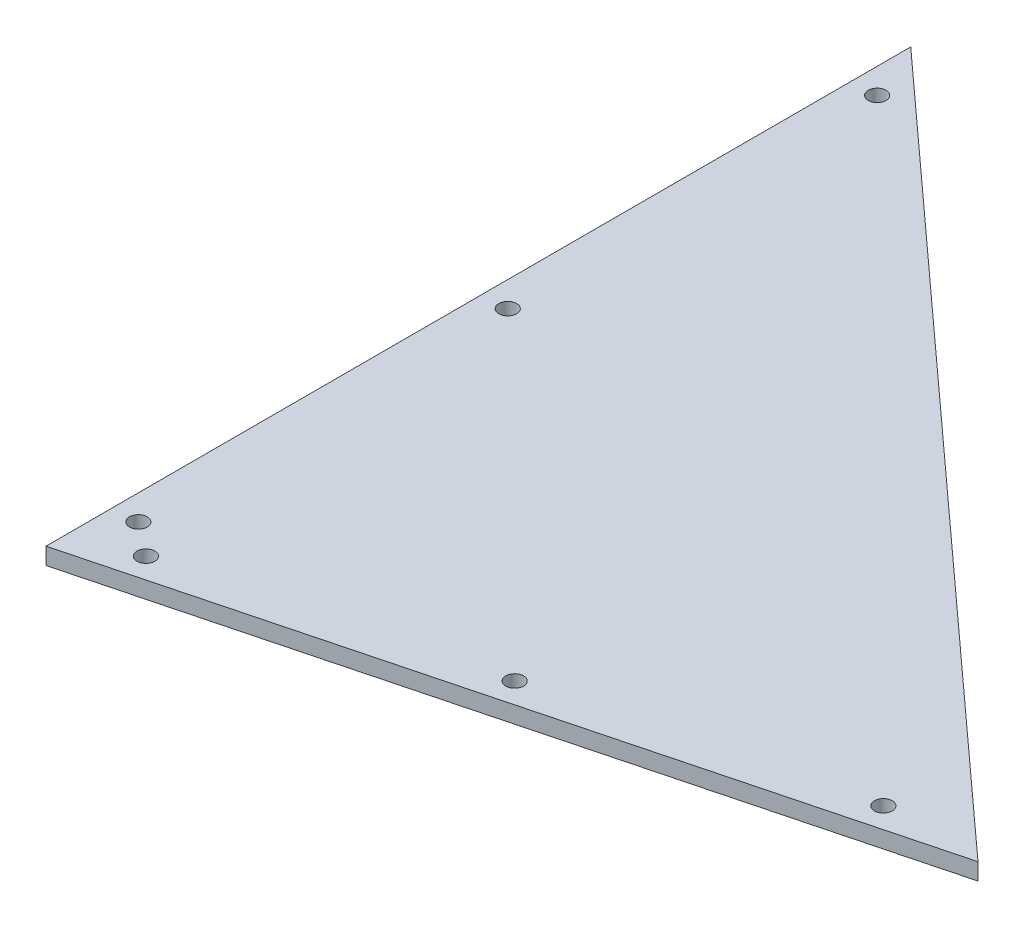
SolidWorks part; units mm, degrees
material "PC High Viscosity"
ref_plane "Front Plane" through (0, 0, 0) normal (0, 0, 1) x (1, 0, 0)
ref_plane "Top Plane" through (0, 0, 0) normal (0, 1, 0) x (1, 0, 0)
ref_plane "Right Plane" through (0, 0, 0) normal (1, 0, 0) x (0, 0, -1)
sketch "Sketch1" plane through (0, 0, 0) normal (0, 1, 0) x (1, 0, 0)
  line L0 (0, 0) -> (0, 327.025)
  line L1 (0, 327.025) -> (279.5805, 72.8863)
  line L2 (279.5805, 72.8863) -> (0, 0)
  dimension "D1" = 327.025
  dimension "D2" = 377.825
  dimension "D3" = 288.925
extrude "Boss-Extrude1" add sketch "Sketch1" along normal blind 6.35
sketch "Sketch2" plane through (0, 6.35, 0) normal (0, 1, 0) x (1, 0, 0)
  line L0 (22.1757, 15.6245) -> (243.3822, 73.2928) construction
  line L1 (9.525, 25.4) -> (9.525, 304.8) construction
  line L2 (0, 0) -> (279.5805, 72.8863) construction
  line L3 (0, 327.025) -> (0, 0) construction
  line L4 (0, 0) -> (12.8152, -49.157) construction
  circle A0 centre (9.525, 25.4) radius 3.3655
  circle A1 centre (9.525, 165.1) radius 3.3655
  circle A2 centre (9.525, 304.8) radius 3.3655
  circle A3 centre (22.1757, 15.6245) radius 3.3655
  circle A4 centre (132.7789, 44.4587) radius 3.3655
  circle A5 centre (243.3822, 73.2928) radius 3.3655
  point P17 (0, 0)
  dimension "D1" = 9.525
  dimension "D3" = 6.731
  dimension "D2" = 9.525
  dimension "D4" = 25.4
  dimension "D5" = 165.1
  dimension "D6" = 304.8
  dimension "D7" = 50.8
  dimension "D8" = 25.4
  dimension "D9" = 139.7
  dimension "D10" = 254
extrude "Cut-Extrude1" cut sketch "Sketch2" against normal through all
